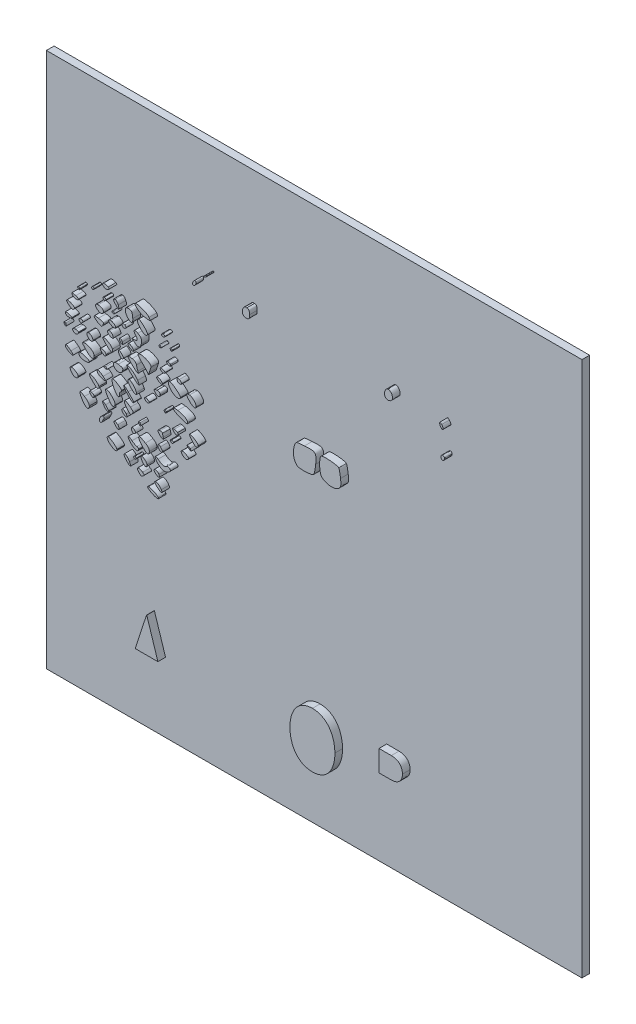
SolidWorks part; units mm, degrees
ref_plane "Plan de face" through (0, 0, 0) normal (0, 0, 1) x (1, 0, 0)
ref_plane "Plan de dessus" through (0, 0, 0) normal (0, 1, 0) x (1, 0, 0)
ref_plane "Plan de droite" through (0, 0, 0) normal (1, 0, 0) x (0, 0, -1)
sketch "Esquisse1" plane through (0, 0, 0) normal (0, 0, 1) x (1, 0, 0)
  line L1 (0, 0) -> (35, 0)
  line L2 (0, 0) -> (0, -35)
  line L3 (0, -35) -> (35, -35)
  line L4 (35, 0) -> (35, -35)
  dimension "D1" = 35
  dimension "D2" = 35
extrude "Boss.-Extru.1" add sketch "Esquisse1" along normal blind 0.5
sketch "Esquisse2" plane through (0, 0, 0) normal (0, 0, -1) x (-1, 0, 0)
  line L0 (-35, 0) -> (0, 0) construction
  line L1 (-35, -35) -> (-35, 0) construction
  line L2 (0, 0) -> (0, -35) construction
  circle A0 centre (-30, -17.5) radius 1
  circle A1 centre (-5, -17.5) radius 1
  dimension "D4" = 2
  dimension "D1" = 17.5
  dimension "D2" = 5
  dimension "D3" = 5
extrude "Boss.-Extru.2" add sketch "Esquisse2" along normal blind 3
chamfer "Chanfrein1" distance 0.5 angle 45 2 edges at (29, -17.5, -3) (4, -17.5, -3)
sketch "Esquisse15" plane through (0, 0, 0.5) normal (0, 0, 1) x (1, 0, 0)
  point P0 (0, 0.001)
  point P1 (0.001, 0.001)
  point P2 (0.001, 0)
ref_plane "Plan7" through (0, 0, 0.5) normal (0, 0, -1) x (-1, 0, 0)
sketch "Esquisse16" plane through (0, 0, 0) normal (0, 0, 1) x (1, 0, 0)
  line L18 (6.2636, -13.0005) -> (6.0872, -13.003)
  line L19 (6.0872, -13.003) -> (6.2675, -13.1533)
  line L37 (7.0433, -28.1853) -> (7.0589, -28.1853)
  line L38 (7.0589, -28.1853) -> (7.7859, -30.4524)
  line L39 (7.7859, -30.4524) -> (6.3006, -30.4524)
  line L40 (6.3006, -30.4524) -> (7.0433, -28.1853)
  line L54 (22.236, -28.1384) -> (23.0412, -28.1384)
  line L55 (23.0412, -29.5221) -> (22.236, -29.5221)
  line L56 (22.236, -29.5221) -> (22.236, -28.1384)
  spline S112 degree 3 poles (7.8123, -21.154) (7.7314, -21.0232) (7.3015, -20.8294) (7.1603, -20.8601) knots 0 0 0 0 1 1 1 1
  spline S113 degree 3 poles (7.1603, -20.8601) (7.0618, -20.8816) (7.0979, -20.9324) (7.3028, -21.0607) knots 0 0 0 0 1 1 1 1
  spline S114 degree 3 poles (7.3028, -21.0607) (7.5848, -21.2371) (7.8992, -21.2947) (7.8123, -21.154) knots 0 0 0 0 1 1 1 1
  spline S115 degree 3 poles (8.0096, -20.6074) (7.9064, -20.4144) (7.6427, -20.2645) (7.5813, -20.3638) knots 0 0 0 0 1 1 1 1
  spline S116 degree 3 poles (7.5813, -20.3638) (7.5356, -20.4378) (7.8945, -20.7624) (8.022, -20.7624) knots 0 0 0 0 1 1 1 1
  spline S117 degree 3 poles (8.022, -20.7624) (8.0608, -20.7624) (8.0553, -20.6926) (8.0096, -20.6074) knots 0 0 0 0 1 1 1 1
  spline S118 degree 3 poles (6.7851, -20.2372) (6.6364, -20.1284) (6.4401, -20.1002) (6.4401, -20.1876) knots 0 0 0 0 1 1 1 1
  spline S119 degree 3 poles (6.4401, -20.1876) (6.4401, -20.2166) (6.4984, -20.3047) (6.5697, -20.3834) knots 0 0 0 0 1 1 1 1
  spline S120 degree 3 poles (6.5697, -20.3834) (6.6725, -20.4971) (6.7225, -20.5073) (6.812, -20.433) knots 0 0 0 0 1 1 1 1
  spline S121 degree 3 poles (6.812, -20.433) (6.9091, -20.3524) (6.9053, -20.325) (6.7851, -20.2372) knots 0 0 0 0 1 1 1 1
  spline S122 degree 3 poles (5.9352, -20.0661) (5.8138, -19.8312) (5.5774, -19.6807) (5.5774, -19.8383) knots 0 0 0 0 1 1 1 1
  spline S123 degree 3 poles (5.5774, -19.8383) (5.5774, -19.9453) (5.889, -20.2919) (5.9852, -20.2919) knots 0 0 0 0 1 1 1 1
  spline S124 degree 3 poles (5.9852, -20.2919) (6.0219, -20.2919) (5.9994, -20.1903) (5.9352, -20.0661) knots 0 0 0 0 1 1 1 1
  spline S125 degree 3 poles (7.8518, -19.8213) (7.7706, -19.6695) (7.5381, -19.5998) (7.5381, -19.7272) knots 0 0 0 0 1 1 1 1
  spline S126 degree 3 poles (7.5381, -19.7272) (7.5381, -19.8259) (7.7158, -19.9781) (7.831, -19.9781) knots 0 0 0 0 1 1 1 1
  spline S127 degree 3 poles (7.831, -19.9781) (7.9115, -19.9781) (7.9163, -19.9417) (7.8518, -19.8213) knots 0 0 0 0 1 1 1 1
  spline S128 degree 3 poles (5.1068, -19.7809) (5.1068, -19.6734) (4.6813, -19.3517) (4.5382, -19.351) knots 0 0 0 0 1 1 1 1
  spline S129 degree 3 poles (4.5382, -19.351) (4.4, -19.3503) (4.4964, -19.5856) (4.6951, -19.7338) knots 0 0 0 0 1 1 1 1
  spline S130 degree 3 poles (4.6951, -19.7338) (4.9526, -19.926) (5.1068, -19.9436) (5.1068, -19.7809) knots 0 0 0 0 1 1 1 1
  spline S131 degree 3 poles (7.0675, -19.6672) (7.0675, -19.5357) (6.8643, -19.3507) (6.7198, -19.3507) knots 0 0 0 0 1 1 1 1
  spline S132 degree 3 poles (6.7198, -19.3507) (6.63, -19.3507) (6.6791, -19.5385) (6.8052, -19.6779) knots 0 0 0 0 1 1 1 1
  spline S133 degree 3 poles (6.8052, -19.6779) (6.9734, -19.8637) (7.0675, -19.8599) (7.0675, -19.6672) knots 0 0 0 0 1 1 1 1
  spline S134 degree 3 poles (6.3617, -19.6644) (6.3617, -19.6213) (6.3264, -19.586) (6.2832, -19.586) knots 0 0 0 0 1 1 1 1
  spline S135 degree 3 poles (6.2832, -19.586) (6.2401, -19.586) (6.2048, -19.6213) (6.2048, -19.6644) knots 0 0 0 0 1 1 1 1
  spline S136 degree 3 poles (6.2048, -19.6644) (6.2048, -19.7076) (6.2401, -19.7428) (6.2832, -19.7428) knots 0 0 0 0 1 1 1 1
  spline S137 degree 3 poles (6.2832, -19.7428) (6.3264, -19.7428) (6.3617, -19.7075) (6.3617, -19.6644) knots 0 0 0 0 1 1 1 1
  spline S138 degree 3 poles (8.539, -19.3307) (8.7003, -19.2016) (8.5056, -19.0192) (8.3261, -19.1313) knots 0 0 0 0 1 1 1 1
  spline S139 degree 3 poles (8.3261, -19.1313) (8.1782, -19.2236) (8.0788, -19.1971) (7.793, -18.9893) knots 0 0 0 0 1 1 1 1
  spline S140 degree 3 poles (7.793, -18.9893) (7.5055, -18.7802) (7.5647, -19.0579) (7.8607, -19.307) knots 0 0 0 0 1 1 1 1
  spline S141 degree 3 poles (7.8607, -19.307) (8.1055, -19.5129) (8.3028, -19.5198) (8.539, -19.3307) knots 0 0 0 0 1 1 1 1
  spline S142 degree 3 poles (6.5185, -19.0762) (6.5185, -19.0115) (6.4704, -18.9586) (6.4115, -18.9586) knots 0 0 0 0 1 1 1 1
  spline S143 degree 3 poles (6.4115, -18.9586) (6.3526, -18.9586) (6.2096, -18.884) (6.0936, -18.7928) knots 0 0 0 0 1 1 1 1
  spline S144 degree 3 poles (6.0936, -18.7928) (5.798, -18.5602) (5.739, -18.6771) (6.0095, -18.9594) knots 0 0 0 0 1 1 1 1
  spline S145 degree 3 poles (6.0095, -18.9594) (6.2487, -19.209) (6.5185, -19.271) (6.5185, -19.0762) knots 0 0 0 0 1 1 1 1
  spline S146 degree 3 poles (7.2244, -18.8398) (7.2244, -18.7014) (7.1483, -18.5961) (6.9695, -18.4871) knots 0 0 0 0 1 1 1 1
  spline S147 degree 3 poles (6.9695, -18.4871) (6.4795, -18.1883) (6.3777, -18.3221) (6.7619, -18.7598) knots 0 0 0 0 1 1 1 1
  spline S148 degree 3 poles (6.7619, -18.7598) (7.0498, -19.0877) (7.2244, -19.1178) (7.2244, -18.8398) knots 0 0 0 0 1 1 1 1
  spline S149 degree 3 poles (4.2049, -18.5664) (4.2984, -18.3856) (4.3032, -18.3311) (4.2258, -18.3311) knots 0 0 0 0 1 1 1 1
  spline S150 degree 3 poles (4.2258, -18.3311) (4.0989, -18.3311) (3.9094, -18.6258) (3.9716, -18.7265) knots 0 0 0 0 1 1 1 1
  spline S151 degree 3 poles (3.9716, -18.7265) (4.0428, -18.8417) (4.0734, -18.8208) (4.2049, -18.5664) knots 0 0 0 0 1 1 1 1
  spline S152 degree 3 poles (5.1628, -18.3535) (5.0974, -18.2881) (4.9984, -18.2496) (4.943, -18.2681) knots 0 0 0 0 1 1 1 1
  spline S153 degree 3 poles (4.943, -18.2681) (4.8728, -18.2915) (4.8988, -18.3583) (5.0284, -18.488) knots 0 0 0 0 1 1 1 1
  spline S154 degree 3 poles (5.0284, -18.488) (5.158, -18.6176) (5.2249, -18.6436) (5.2483, -18.5734) knots 0 0 0 0 1 1 1 1
  spline S155 degree 3 poles (5.2483, -18.5734) (5.2668, -18.518) (5.2283, -18.419) (5.1628, -18.3535) knots 0 0 0 0 1 1 1 1
  spline S156 degree 3 poles (8.0871, -18.4151) (8.0871, -18.3751) (8.0269, -18.2821) (7.9534, -18.2086) knots 0 0 0 0 1 1 1 1
  spline S157 degree 3 poles (7.9534, -18.2086) (7.7935, -18.0487) (7.7056, -18.1942) (7.854, -18.373) knots 0 0 0 0 1 1 1 1
  spline S158 degree 3 poles (7.854, -18.373) (7.9615, -18.5025) (8.0871, -18.5252) (8.0871, -18.4151) knots 0 0 0 0 1 1 1 1
  spline S159 degree 3 poles (3.303, -18.2274) (3.303, -18.1014) (3.2062, -17.9819) (2.9892, -17.8399) knots 0 0 0 0 1 1 1 1
  spline S160 degree 3 poles (2.9892, -17.8399) (2.6678, -17.6294) (2.6082, -17.6622) (2.764, -17.9637) knots 0 0 0 0 1 1 1 1
  spline S161 degree 3 poles (2.764, -17.9637) (2.9922, -18.4054) (3.303, -18.5574) (3.303, -18.2274) knots 0 0 0 0 1 1 1 1
  spline S162 degree 3 poles (6.317, -18.2616) (6.3682, -18.1787) (6.1434, -17.9743) (6.0756, -18.0421) knots 0 0 0 0 1 1 1 1
  spline S163 degree 3 poles (6.0756, -18.0421) (6.0102, -18.1074) (6.1048, -18.3311) (6.1977, -18.3311) knots 0 0 0 0 1 1 1 1
  spline S164 degree 3 poles (6.1977, -18.3311) (6.2397, -18.3311) (6.2933, -18.2998) (6.317, -18.2616) knots 0 0 0 0 1 1 1 1
  spline S165 degree 3 poles (9.7885, -17.9721) (9.8228, -17.8691) (9.4394, -17.6827) (9.331, -17.7497) knots 0 0 0 0 1 1 1 1
  spline S166 degree 3 poles (9.331, -17.7497) (9.2228, -17.8166) (9.4993, -18.1073) (9.6444, -18.0791) knots 0 0 0 0 1 1 1 1
  spline S167 degree 3 poles (9.6444, -18.0791) (9.7081, -18.0668) (9.773, -18.0186) (9.7885, -17.9721) knots 0 0 0 0 1 1 1 1
  spline S168 degree 3 poles (4.5578, -17.8742) (4.5578, -17.8386) (4.4696, -17.7266) (4.3617, -17.6253) knots 0 0 0 0 1 1 1 1
  spline S169 degree 3 poles (4.3617, -17.6253) (4.1425, -17.4193) (4.1008, -17.4978) (4.2878, -17.7647) knots 0 0 0 0 1 1 1 1
  spline S170 degree 3 poles (4.2878, -17.7647) (4.4091, -17.9378) (4.5578, -17.9982) (4.5578, -17.8742) knots 0 0 0 0 1 1 1 1
  spline S171 degree 3 poles (6.6113, -17.5298) (6.5551, -17.4736) (6.5185, -17.4689) (6.5185, -17.5181) knots 0 0 0 0 1 1 1 1
  spline S172 degree 3 poles (6.5185, -17.5181) (6.5185, -17.6228) (6.6113, -17.7155) (6.6636, -17.6632) knots 0 0 0 0 1 1 1 1
  spline S173 degree 3 poles (6.6636, -17.6632) (6.6859, -17.6409) (6.6624, -17.5809) (6.6113, -17.5298) knots 0 0 0 0 1 1 1 1
  spline S174 degree 3 poles (8.1347, -17.5796) (8.1085, -17.5114) (8.0871, -17.4232) (8.0871, -17.3836) knots 0 0 0 0 1 1 1 1
  spline S175 degree 3 poles (8.0871, -17.3836) (8.0871, -17.344) (8.0165, -17.3116) (7.9303, -17.3116) knots 0 0 0 0 1 1 1 1
  spline S176 degree 3 poles (7.9303, -17.3116) (7.7394, -17.3116) (7.7328, -17.372) (7.9032, -17.5603) knots 0 0 0 0 1 1 1 1
  spline S177 degree 3 poles (7.9032, -17.5603) (8.0627, -17.7365) (8.1993, -17.7479) (8.1347, -17.5796) knots 0 0 0 0 1 1 1 1
  spline S178 degree 3 poles (3.6167, -17.5168) (3.6167, -17.4571) (3.5461, -17.3898) (3.4598, -17.3673) knots 0 0 0 0 1 1 1 1
  spline S179 degree 3 poles (3.4598, -17.3673) (3.2832, -17.3211) (3.2565, -17.3906) (3.3971, -17.5311) knots 0 0 0 0 1 1 1 1
  spline S180 degree 3 poles (3.3971, -17.5311) (3.5224, -17.6564) (3.6167, -17.6503) (3.6167, -17.5168) knots 0 0 0 0 1 1 1 1
  spline S181 degree 3 poles (5.716, -17.4684) (5.6199, -17.3144) (5.4205, -17.2509) (5.4205, -17.3743) knots 0 0 0 0 1 1 1 1
  spline S182 degree 3 poles (5.4205, -17.3743) (5.4205, -17.4723) (5.5978, -17.6253) (5.7114, -17.6253) knots 0 0 0 0 1 1 1 1
  spline S183 degree 3 poles (5.7114, -17.6253) (5.7944, -17.6253) (5.7953, -17.5952) (5.716, -17.4684) knots 0 0 0 0 1 1 1 1
  spline S184 degree 3 poles (8.793, -17.5468) (8.793, -17.5037) (8.7379, -17.4684) (8.6707, -17.4684) knots 0 0 0 0 1 1 1 1
  spline S185 degree 3 poles (8.6707, -17.4684) (8.6034, -17.4684) (8.5702, -17.5037) (8.5969, -17.5468) knots 0 0 0 0 1 1 1 1
  spline S186 degree 3 poles (8.5969, -17.5468) (8.6235, -17.59) (8.6786, -17.6253) (8.7192, -17.6253) knots 0 0 0 0 1 1 1 1
  spline S187 degree 3 poles (8.7192, -17.6253) (8.7598, -17.6253) (8.793, -17.59) (8.793, -17.5468) knots 0 0 0 0 1 1 1 1
  spline S188 degree 3 poles (4.983, -17.3386) (5.059, -17.1406) (4.4761, -16.5775) (4.3711, -16.7475) knots 0 0 0 0 1 1 1 1
  spline S189 degree 3 poles (4.3711, -16.7475) (4.3117, -16.8436) (4.708, -17.4684) (4.8284, -17.4684) knots 0 0 0 0 1 1 1 1
  spline S190 degree 3 poles (4.8284, -17.4684) (4.886, -17.4684) (4.9556, -17.41) (4.983, -17.3386) knots 0 0 0 0 1 1 1 1
  spline S191 degree 3 poles (9.891, -17.3508) (9.8373, -17.2861) (9.7535, -17.2342) (9.7049, -17.2356) knots 0 0 0 0 1 1 1 1
  spline S192 degree 3 poles (9.7049, -17.2356) (9.6563, -17.237) (9.685, -17.2899) (9.7687, -17.3533) knots 0 0 0 0 1 1 1 1
  spline S193 degree 3 poles (9.7687, -17.3533) (9.9643, -17.5012) (10.0149, -17.5001) (9.891, -17.3508) knots 0 0 0 0 1 1 1 1
  spline S194 degree 3 poles (5.9899, -16.9454) (5.5762, -16.6067) (5.4424, -16.747) (5.7878, -17.1574) knots 0 0 0 0 1 1 1 1
  spline S195 degree 3 poles (5.7878, -17.1574) (5.9853, -17.3922) (6.0045, -17.3987) (6.1022, -17.265) knots 0 0 0 0 1 1 1 1
  spline S196 degree 3 poles (6.1022, -17.265) (6.1933, -17.1404) (6.1793, -17.1005) (5.9899, -16.9454) knots 0 0 0 0 1 1 1 1
  spline S197 degree 3 poles (2.5797, -16.9129) (2.6011, -16.8013) (2.3103, -16.6057) (2.1228, -16.6057) knots 0 0 0 0 1 1 1 1
  spline S198 degree 3 poles (2.1228, -16.6057) (2.0056, -16.6057) (2.0352, -16.7752) (2.1805, -16.9358) knots 0 0 0 0 1 1 1 1
  spline S199 degree 3 poles (2.1805, -16.9358) (2.3329, -17.1042) (2.5452, -17.092) (2.5797, -16.9129) knots 0 0 0 0 1 1 1 1
  spline S200 degree 3 poles (9.0717, -16.8478) (9.0427, -16.8009) (8.945, -16.7626) (8.8546, -16.7626) knots 0 0 0 0 1 1 1 1
  spline S201 degree 3 poles (8.8546, -16.7626) (8.6945, -16.7626) (8.694, -16.7667) (8.8339, -16.9213) knots 0 0 0 0 1 1 1 1
  spline S202 degree 3 poles (8.8339, -16.9213) (8.9784, -17.081) (9.1778, -17.0195) (9.0717, -16.8478) knots 0 0 0 0 1 1 1 1
  spline S203 degree 3 poles (10.4225, -16.9123) (10.4444, -16.7992) (9.9255, -16.4666) (9.8481, -16.5441) knots 0 0 0 0 1 1 1 1
  spline S204 degree 3 poles (9.8481, -16.5441) (9.825, -16.5671) (9.9001, -16.6978) (10.0151, -16.8344) knots 0 0 0 0 1 1 1 1
  spline S205 degree 3 poles (10.0151, -16.8344) (10.2269, -17.0861) (10.3829, -17.1159) (10.4225, -16.9123) knots 0 0 0 0 1 1 1 1
  spline S206 degree 3 poles (3.9304, -16.8119) (3.9304, -16.6791) (3.4806, -16.3542) (3.3395, -16.385) knots 0 0 0 0 1 1 1 1
  spline S207 degree 3 poles (3.3395, -16.385) (3.2601, -16.4023) (3.3098, -16.4977) (3.5059, -16.7048) knots 0 0 0 0 1 1 1 1
  spline S208 degree 3 poles (3.5059, -16.7048) (3.7721, -16.9859) (3.9304, -17.0259) (3.9304, -16.8119) knots 0 0 0 0 1 1 1 1
  spline S209 degree 3 poles (5.2637, -16.6104) (5.2637, -16.5266) (5.299, -16.4363) (5.3421, -16.4097) knots 0 0 0 0 1 1 1 1
  spline S210 degree 3 poles (5.3421, -16.4097) (5.3852, -16.383) (5.4205, -16.3274) (5.4205, -16.2862) knots 0 0 0 0 1 1 1 1
  spline S211 degree 3 poles (5.4205, -16.2862) (5.4205, -16.2113) (4.9631, -15.9007) (4.8519, -15.9002) knots 0 0 0 0 1 1 1 1
  spline S212 degree 3 poles (4.8519, -15.9002) (4.7305, -15.8995) (4.7995, -16.2525) (4.9696, -16.5023) knots 0 0 0 0 1 1 1 1
  spline S213 degree 3 poles (4.9696, -16.5023) (5.1702, -16.797) (5.2637, -16.8313) (5.2637, -16.6104) knots 0 0 0 0 1 1 1 1
  spline S214 degree 3 poles (6.2048, -16.5586) (6.2048, -16.5328) (6.0442, -16.3486) (5.8478, -16.1494) knots 0 0 0 0 1 1 1 1
  spline S215 degree 3 poles (5.8478, -16.1494) (5.4547, -15.7507) (5.4471, -15.933) (5.8394, -16.3508) knots 0 0 0 0 1 1 1 1
  spline S216 degree 3 poles (5.8394, -16.3508) (6.0625, -16.5884) (6.2048, -16.6694) (6.2048, -16.5586) knots 0 0 0 0 1 1 1 1
  spline S217 degree 3 poles (4.2049, -16.0935) (3.9356, -15.8728) (3.7554, -15.8398) (3.8261, -16.0241) knots 0 0 0 0 1 1 1 1
  spline S218 degree 3 poles (3.8261, -16.0241) (3.8756, -16.1531) (4.1187, -16.2805) (4.3225, -16.2842) knots 0 0 0 0 1 1 1 1
  spline S219 degree 3 poles (4.3225, -16.2842) (4.3939, -16.2855) (4.3476, -16.2105) (4.2049, -16.0935) knots 0 0 0 0 1 1 1 1
  spline S220 degree 3 poles (7.2244, -16.0651) (7.2244, -15.9856) (6.9855, -15.8773) (6.9308, -15.932) knots 0 0 0 0 1 1 1 1
  spline S221 degree 3 poles (6.9308, -15.932) (6.9111, -15.9517) (6.9182, -16.0055) (6.9467, -16.0515) knots 0 0 0 0 1 1 1 1
  spline S222 degree 3 poles (6.9467, -16.0515) (7.0092, -16.1527) (7.2244, -16.1633) (7.2244, -16.0651) knots 0 0 0 0 1 1 1 1
  spline S223 degree 3 poles (8.3224, -16.0567) (8.3224, -16.0135) (8.285, -15.9783) (8.2393, -15.9783) knots 0 0 0 0 1 1 1 1
  spline S224 degree 3 poles (8.2393, -15.9783) (8.1937, -15.9783) (8.1781, -16.0135) (8.2047, -16.0567) knots 0 0 0 0 1 1 1 1
  spline S225 degree 3 poles (8.2047, -16.0567) (8.2314, -16.0998) (8.2688, -16.1351) (8.2878, -16.1351) knots 0 0 0 0 1 1 1 1
  spline S226 degree 3 poles (8.2878, -16.1351) (8.3068, -16.1351) (8.3224, -16.0998) (8.3224, -16.0567) knots 0 0 0 0 1 1 1 1
  spline S227 degree 3 poles (6.3867, -15.9194) (6.3164, -15.72) (6.0375, -15.4293) (5.9166, -15.4293) knots 0 0 0 0 1 1 1 1
  spline S228 degree 3 poles (5.9166, -15.4293) (5.751, -15.4293) (5.7954, -15.5987) (6.0234, -15.8367) knots 0 0 0 0 1 1 1 1
  spline S229 degree 3 poles (6.0234, -15.8367) (6.2622, -16.086) (6.4615, -16.1314) (6.3867, -15.9194) knots 0 0 0 0 1 1 1 1
  spline S230 degree 3 poles (9.7341, -15.9418) (9.7341, -15.7989) (9.4727, -15.6539) (9.0871, -15.5829) knots 0 0 0 0 1 1 1 1
  spline S231 degree 3 poles (9.0871, -15.5829) (8.6359, -15.4998) (8.7131, -15.7013) (9.2047, -15.8903) knots 0 0 0 0 1 1 1 1
  spline S232 degree 3 poles (9.2047, -15.8903) (9.7072, -16.0834) (9.7341, -16.086) (9.7341, -15.9418) knots 0 0 0 0 1 1 1 1
  spline S233 degree 3 poles (2.1026, -15.7013) (1.8737, -15.5) (1.7344, -15.4547) (1.7344, -15.5817) knots 0 0 0 0 1 1 1 1
  spline S234 degree 3 poles (1.7344, -15.5817) (1.7344, -15.6834) (2.0563, -15.9004) (2.2028, -15.8974) knots 0 0 0 0 1 1 1 1
  spline S235 degree 3 poles (2.2028, -15.8974) (2.2844, -15.8957) (2.2523, -15.833) (2.1026, -15.7013) knots 0 0 0 0 1 1 1 1
  spline S236 degree 3 poles (3.303, -15.723) (3.303, -15.597) (2.7398, -15.4145) (2.6436, -15.5093) knots 0 0 0 0 1 1 1 1
  spline S237 degree 3 poles (2.6436, -15.5093) (2.601, -15.5512) (2.6128, -15.6282) (2.6728, -15.7004) knots 0 0 0 0 1 1 1 1
  spline S238 degree 3 poles (2.6728, -15.7004) (2.7944, -15.8469) (3.303, -15.8651) (3.303, -15.723) knots 0 0 0 0 1 1 1 1
  spline S239 degree 3 poles (4.4794, -15.5553) (4.4794, -15.5383) (4.4264, -15.5042) (4.3617, -15.4793) knots 0 0 0 0 1 1 1 1
  spline S240 degree 3 poles (4.3617, -15.4793) (4.297, -15.4545) (4.2441, -15.4684) (4.2441, -15.5101) knots 0 0 0 0 1 1 1 1
  spline S241 degree 3 poles (4.2441, -15.5101) (4.2441, -15.5519) (4.297, -15.5861) (4.3617, -15.5861) knots 0 0 0 0 1 1 1 1
  spline S242 degree 3 poles (4.3617, -15.5861) (4.4265, -15.5861) (4.4794, -15.5722) (4.4794, -15.5553) knots 0 0 0 0 1 1 1 1
  spline S243 degree 3 poles (3.6167, -15.2352) (3.6167, -15.0129) (3.248, -14.7763) (2.9643, -14.8167) knots 0 0 0 0 1 1 1 1
  spline S244 degree 3 poles (2.9643, -14.8167) (2.8024, -14.8397) (2.8079, -14.8568) (3.0677, -15.1337) knots 0 0 0 0 1 1 1 1
  spline S245 degree 3 poles (3.0677, -15.1337) (3.392, -15.4794) (3.6167, -15.521) (3.6167, -15.2352) knots 0 0 0 0 1 1 1 1
  spline S246 degree 3 poles (6.4641, -15.1886) (6.3099, -14.9266) (5.8377, -14.5927) (5.7497, -14.6835) knots 0 0 0 0 1 1 1 1
  spline S247 degree 3 poles (5.7497, -14.6835) (5.6936, -14.7414) (6.4229, -15.4293) (6.5404, -15.4293) knots 0 0 0 0 1 1 1 1
  spline S248 degree 3 poles (6.5404, -15.4293) (6.5764, -15.4293) (6.5421, -15.3209) (6.4641, -15.1886) knots 0 0 0 0 1 1 1 1
  spline S249 degree 3 poles (7.9302, -15.2724) (7.9302, -15.1574) (7.878, -15.1155) (7.7342, -15.1155) knots 0 0 0 0 1 1 1 1
  spline S250 degree 3 poles (7.7342, -15.1155) (7.5201, -15.1155) (7.486, -15.1889) (7.6322, -15.3351) knots 0 0 0 0 1 1 1 1
  spline S251 degree 3 poles (7.6322, -15.3351) (7.7765, -15.4795) (7.9302, -15.4471) (7.9302, -15.2724) knots 0 0 0 0 1 1 1 1
  spline S252 degree 3 poles (5.4616, -15.1881) (5.525, -14.9883) (5.5103, -14.9727) (5.2003, -14.9107) knots 0 0 0 0 1 1 1 1
  spline S253 degree 3 poles (5.2003, -14.9107) (4.9181, -14.8543) (4.7819, -15.0307) (4.9508, -15.2342) knots 0 0 0 0 1 1 1 1
  spline S254 degree 3 poles (4.9508, -15.2342) (5.0954, -15.4085) (5.4004, -15.3809) (5.4616, -15.1881) knots 0 0 0 0 1 1 1 1
  spline S255 degree 3 poles (4.401, -14.7679) (4.401, -14.6456) (4.1081, -14.5195) (4.0226, -14.605) knots 0 0 0 0 1 1 1 1
  spline S256 degree 3 poles (4.0226, -14.605) (3.9688, -14.6588) (4.2222, -14.8803) (4.3375, -14.8803) knots 0 0 0 0 1 1 1 1
  spline S257 degree 3 poles (4.3375, -14.8803) (4.3724, -14.8803) (4.401, -14.8297) (4.401, -14.7679) knots 0 0 0 0 1 1 1 1
  spline S258 degree 3 poles (9.2635, -14.7631) (9.2635, -14.6251) (8.648, -14.1577) (8.5479, -14.2196) knots 0 0 0 0 1 1 1 1
  spline S259 degree 3 poles (8.5479, -14.2196) (8.4241, -14.2961) (8.4758, -14.4918) (8.6718, -14.6877) knots 0 0 0 0 1 1 1 1
  spline S260 degree 3 poles (8.6718, -14.6877) (8.8866, -14.9025) (9.2635, -14.9505) (9.2635, -14.7631) knots 0 0 0 0 1 1 1 1
  spline S261 degree 3 poles (10.2831, -14.78) (10.2831, -14.5839) (10.0378, -14.3312) (9.8473, -14.3312) knots 0 0 0 0 1 1 1 1
  spline S262 degree 3 poles (9.8473, -14.3312) (9.6055, -14.3312) (9.6056, -14.4112) (9.848, -14.6727) knots 0 0 0 0 1 1 1 1
  spline S263 degree 3 poles (9.848, -14.6727) (10.0509, -14.8916) (10.2831, -14.9489) (10.2831, -14.78) knots 0 0 0 0 1 1 1 1
  spline S264 degree 3 poles (6.4776, -14.6645) (6.4459, -14.589) (6.4034, -14.4516) (6.3832, -14.3591) knots 0 0 0 0 1 1 1 1
  spline S265 degree 3 poles (6.3832, -14.3591) (6.3588, -14.2471) (6.2663, -14.1749) (6.1063, -14.1429) knots 0 0 0 0 1 1 1 1
  spline S266 degree 3 poles (6.1063, -14.1429) (5.7488, -14.0714) (5.745, -14.1491) (6.09, -14.4814) knots 0 0 0 0 1 1 1 1
  spline S267 degree 3 poles (6.09, -14.4814) (6.4327, -14.8116) (6.5659, -14.8746) (6.4776, -14.6645) knots 0 0 0 0 1 1 1 1
  spline S268 degree 3 poles (2.5971, -14.4) (2.5971, -14.3622) (2.5089, -14.3312) (2.401, -14.3312) knots 0 0 0 0 1 1 1 1
  spline S269 degree 3 poles (2.401, -14.3312) (2.1878, -14.3312) (2.1528, -14.4046) (2.2972, -14.5489) knots 0 0 0 0 1 1 1 1
  spline S270 degree 3 poles (2.2972, -14.5489) (2.3934, -14.6451) (2.5971, -14.5439) (2.5971, -14.4) knots 0 0 0 0 1 1 1 1
  spline S271 degree 3 poles (8.0871, -14.5692) (8.0871, -14.4685) (7.7741, -14.3044) (7.708, -14.3705) knots 0 0 0 0 1 1 1 1
  spline S272 degree 3 poles (7.708, -14.3705) (7.6794, -14.3991) (7.7244, -14.4725) (7.8081, -14.5337) knots 0 0 0 0 1 1 1 1
  spline S273 degree 3 poles (7.8081, -14.5337) (7.9852, -14.6632) (8.0871, -14.6762) (8.0871, -14.5692) knots 0 0 0 0 1 1 1 1
  spline S274 degree 3 poles (7.3347, -14.0135) (7.4226, -13.8053) (6.607, -13.4972) (6.486, -13.6929) knots 0 0 0 0 1 1 1 1
  spline S275 degree 3 poles (6.486, -13.6929) (6.463, -13.7301) (6.6021, -13.9085) (6.7951, -14.0894) knots 0 0 0 0 1 1 1 1
  spline S276 degree 3 poles (6.7951, -14.0894) (6.9881, -14.2703) (7.1496, -14.4604) (7.154, -14.512) knots 0 0 0 0 1 1 1 1
  spline S277 degree 3 poles (7.154, -14.512) (7.1584, -14.5635) (7.1893, -14.4998) (7.2227, -14.3704) knots 0 0 0 0 1 1 1 1
  spline S278 degree 3 poles (7.2227, -14.3704) (7.2561, -14.241) (7.3065, -14.0804) (7.3347, -14.0135) knots 0 0 0 0 1 1 1 1
  spline S279 degree 3 poles (1.7488, -14.3142) (1.6925, -14.2579) (1.656, -14.2533) (1.656, -14.3024) knots 0 0 0 0 1 1 1 1
  spline S280 degree 3 poles (1.656, -14.3024) (1.656, -14.4071) (1.7487, -14.4999) (1.8011, -14.4475) knots 0 0 0 0 1 1 1 1
  spline S281 degree 3 poles (1.8011, -14.4475) (1.8233, -14.4253) (1.7999, -14.3653) (1.7488, -14.3142) knots 0 0 0 0 1 1 1 1
  spline S282 degree 3 poles (3.5382, -14.3861) (3.5382, -14.2549) (3.3792, -14.0959) (3.2481, -14.0959) knots 0 0 0 0 1 1 1 1
  spline S283 degree 3 poles (3.2481, -14.0959) (3.1201, -14.0959) (3.1156, -14.2693) (3.2402, -14.3939) knots 0 0 0 0 1 1 1 1
  spline S284 degree 3 poles (3.2402, -14.3939) (3.3648, -14.5186) (3.5382, -14.514) (3.5382, -14.3861) knots 0 0 0 0 1 1 1 1
  spline S285 degree 3 poles (4.8141, -14.2463) (4.7674, -14.0678) (4.2824, -13.7954) (4.1863, -13.8936) knots 0 0 0 0 1 1 1 1
  spline S286 degree 3 poles (4.1863, -13.8936) (4.116, -13.9654) (4.7076, -14.5017) (4.7965, -14.4468) knots 0 0 0 0 1 1 1 1
  spline S287 degree 3 poles (4.7965, -14.4468) (4.8297, -14.4262) (4.8376, -14.336) (4.8141, -14.2463) knots 0 0 0 0 1 1 1 1
  spline S288 degree 3 poles (5.5317, -14.4201) (5.5815, -14.3395) (5.2831, -14.0503) (5.2176, -14.1158) knots 0 0 0 0 1 1 1 1
  spline S289 degree 3 poles (5.2176, -14.1158) (5.1583, -14.1752) (5.3272, -14.4881) (5.4187, -14.4881) knots 0 0 0 0 1 1 1 1
  spline S290 degree 3 poles (5.4187, -14.4881) (5.4577, -14.4881) (5.5086, -14.4575) (5.5317, -14.4201) knots 0 0 0 0 1 1 1 1
  spline S291 degree 3 poles (9.342, -13.9418) (9.342, -13.9002) (9.2714, -13.8284) (9.1851, -13.7822) knots 0 0 0 0 1 1 1 1
  spline S292 degree 3 poles (9.1851, -13.7822) (9.0638, -13.7173) (9.0282, -13.7226) (9.0282, -13.8056) knots 0 0 0 0 1 1 1 1
  spline S293 degree 3 poles (9.0282, -13.8056) (9.0282, -13.8646) (9.0518, -13.9364) (9.0805, -13.9652) knots 0 0 0 0 1 1 1 1
  spline S294 degree 3 poles (9.0805, -13.9652) (9.1595, -14.0442) (9.342, -14.0279) (9.342, -13.9418) knots 0 0 0 0 1 1 1 1
  spline S295 degree 3 poles (8.244, -13.869) (8.244, -13.7895) (8.0051, -13.6812) (7.9504, -13.7359) knots 0 0 0 0 1 1 1 1
  spline S296 degree 3 poles (7.9504, -13.7359) (7.9307, -13.7556) (7.9378, -13.8094) (7.9662, -13.8554) knots 0 0 0 0 1 1 1 1
  spline S297 degree 3 poles (7.9662, -13.8554) (8.0288, -13.9567) (8.244, -13.9672) (8.244, -13.869) knots 0 0 0 0 1 1 1 1
  spline S298 degree 3 poles (2.1618, -13.791) (2.0466, -13.6834) (1.7344, -13.6062) (1.7344, -13.6854) knots 0 0 0 0 1 1 1 1
  spline S299 degree 3 poles (1.7344, -13.6854) (1.7344, -13.8052) (1.8304, -13.8606) (2.0376, -13.8606) knots 0 0 0 0 1 1 1 1
  spline S300 degree 3 poles (2.0376, -13.8606) (2.157, -13.8606) (2.2066, -13.8328) (2.1618, -13.791) knots 0 0 0 0 1 1 1 1
  spline S301 degree 3 poles (2.8683, -13.7092) (2.9263, -13.6153) (2.7787, -13.5224) (2.6743, -13.5869) knots 0 0 0 0 1 1 1 1
  spline S302 degree 3 poles (2.6743, -13.5869) (2.5865, -13.6411) (2.6441, -13.7822) (2.754, -13.7822) knots 0 0 0 0 1 1 1 1
  spline S303 degree 3 poles (2.754, -13.7822) (2.792, -13.7822) (2.8434, -13.7493) (2.8683, -13.7092) knots 0 0 0 0 1 1 1 1
  spline S304 degree 3 poles (5.4532, -13.5189) (5.4028, -13.3875) (5.2637, -13.339) (5.2637, -13.4528) knots 0 0 0 0 1 1 1 1
  spline S305 degree 3 poles (5.2637, -13.4528) (5.2637, -13.5291) (5.4386, -13.7118) (5.476, -13.6745) knots 0 0 0 0 1 1 1 1
  spline S306 degree 3 poles (5.476, -13.6745) (5.4906, -13.6598) (5.4804, -13.5898) (5.4532, -13.5189) knots 0 0 0 0 1 1 1 1
  spline S307 degree 3 poles (6.1871, -13.6113) (6.1416, -13.4748) (5.9082, -13.3468) (5.8362, -13.4188) knots 0 0 0 0 1 1 1 1
  spline S308 degree 3 poles (5.8362, -13.4188) (5.8018, -13.4532) (5.8422, -13.5314) (5.9258, -13.5925) knots 0 0 0 0 1 1 1 1
  spline S309 degree 3 poles (5.9258, -13.5925) (6.1109, -13.7278) (6.2287, -13.7363) (6.1871, -13.6113) knots 0 0 0 0 1 1 1 1
  spline S310 degree 3 poles (4.8715, -13.5925) (4.8715, -13.4508) (4.7508, -13.3116) (4.6279, -13.3116) knots 0 0 0 0 1 1 1 1
  spline S311 degree 3 poles (4.6279, -13.3116) (4.4578, -13.3116) (4.4372, -13.3949) (4.5735, -13.5312) knots 0 0 0 0 1 1 1 1
  spline S312 degree 3 poles (4.5735, -13.5312) (4.6625, -13.6202) (4.8715, -13.6632) (4.8715, -13.5925) knots 0 0 0 0 1 1 1 1
  spline S313 degree 3 poles (8.5935, -13.2278) (8.5687, -13.1876) (8.4932, -13.1548) (8.4258, -13.1548) knots 0 0 0 0 1 1 1 1
  spline S314 degree 3 poles (8.4258, -13.1548) (8.3261, -13.1548) (8.3213, -13.1766) (8.4001, -13.2715) knots 0 0 0 0 1 1 1 1
  spline S315 degree 3 poles (8.4001, -13.2715) (8.5014, -13.3936) (8.6721, -13.3549) (8.5935, -13.2278) knots 0 0 0 0 1 1 1 1
  spline S316 degree 3 poles (2.3403, -13.1802) (2.3736, -13.0802) (1.9093, -12.8752) (1.8299, -12.9549) knots 0 0 0 0 1 1 1 1
  spline S317 degree 3 poles (1.8299, -12.9549) (1.7595, -13.0255) (2.1208, -13.3266) (2.2315, -13.2897) knots 0 0 0 0 1 1 1 1
  spline S318 degree 3 poles (2.2315, -13.2897) (2.2762, -13.2748) (2.3252, -13.2255) (2.3403, -13.1802) knots 0 0 0 0 1 1 1 1
  spline S319 degree 3 poles (4.1983, -13.1827) (4.2607, -13.0202) (4.2643, -13.023) (3.9007, -12.955) knots 0 0 0 0 1 1 1 1
  spline S320 degree 3 poles (3.9007, -12.955) (3.6593, -12.9099) (3.6039, -12.9206) (3.6324, -13.0068) knots 0 0 0 0 1 1 1 1
  spline S321 degree 3 poles (3.6324, -13.0068) (3.665, -13.1055) (3.9753, -13.3076) (4.0985, -13.3104) knots 0 0 0 0 1 1 1 1
  spline S322 degree 3 poles (4.0985, -13.3104) (4.1262, -13.311) (4.1712, -13.2536) (4.1983, -13.1827) knots 0 0 0 0 1 1 1 1
  spline S323 degree 3 poles (6.6984, -13.0171) (6.7502, -12.7461) (6.706, -12.6486) (6.4753, -12.5251) knots 0 0 0 0 1 1 1 1
  spline S324 degree 3 poles (6.4753, -12.5251) (6.234, -12.396) (6.1379, -12.4802) (6.3099, -12.6702) knots 0 0 0 0 1 1 1 1
  spline S325 degree 3 poles (6.3099, -12.6702) (6.4904, -12.8697) (6.4725, -12.9974) (6.2636, -13.0005) knots 0 0 0 0 1 1 1 1
  spline S326 degree 3 poles (6.2675, -13.1533) (6.4892, -13.3382) (6.6465, -13.2885) (6.6984, -13.0171) knots 0 0 0 0 1 1 1 1
  spline S327 degree 3 poles (5.0284, -12.9351) (5.0284, -12.8243) (4.8445, -12.6842) (4.699, -12.6842) knots 0 0 0 0 1 1 1 1
  spline S328 degree 3 poles (4.699, -12.6842) (4.519, -12.6842) (4.5169, -12.8094) (4.6951, -12.9132) knots 0 0 0 0 1 1 1 1
  spline S329 degree 3 poles (4.6951, -12.9132) (4.8613, -13.0099) (5.0284, -13.0209) (5.0284, -12.9351) knots 0 0 0 0 1 1 1 1
  spline S330 degree 3 poles (5.6954, -12.6051) (5.7222, -12.5617) (5.6875, -12.5044) (5.6182, -12.4778) knots 0 0 0 0 1 1 1 1
  spline S331 degree 3 poles (5.6182, -12.4778) (5.468, -12.4202) (5.3843, -12.4837) (5.4565, -12.6005) knots 0 0 0 0 1 1 1 1
  spline S332 degree 3 poles (5.4565, -12.6005) (5.5217, -12.7059) (5.6318, -12.708) (5.6954, -12.6051) knots 0 0 0 0 1 1 1 1
  spline S333 degree 3 poles (2.5971, -12.5365) (2.5971, -12.4983) (2.5177, -12.4459) (2.4206, -12.4199) knots 0 0 0 0 1 1 1 1
  spline S334 degree 3 poles (2.4206, -12.4199) (2.1459, -12.3463) (2.0995, -12.361) (2.205, -12.4881) knots 0 0 0 0 1 1 1 1
  spline S335 degree 3 poles (2.205, -12.4881) (2.3102, -12.6149) (2.5971, -12.6503) (2.5971, -12.5365) knots 0 0 0 0 1 1 1 1
  spline S336 degree 3 poles (4.2188, -12.4802) (4.2751, -12.3334) (4.1221, -12.2165) (3.8716, -12.2148) knots 0 0 0 0 1 1 1 1
  spline S337 degree 3 poles (3.8716, -12.2148) (3.6609, -12.2133) (3.6417, -12.3518) (3.8324, -12.4966) knots 0 0 0 0 1 1 1 1
  spline S338 degree 3 poles (3.8324, -12.4966) (4.0181, -12.6375) (4.1607, -12.6315) (4.2188, -12.4802) knots 0 0 0 0 1 1 1 1
  spline S339 degree 3 poles (8.0087, -12.5712) (8.0087, -12.5521) (7.9734, -12.5148) (7.9302, -12.4881) knots 0 0 0 0 1 1 1 1
  spline S340 degree 3 poles (7.9302, -12.4881) (7.8871, -12.4614) (7.8518, -12.477) (7.8518, -12.5227) knots 0 0 0 0 1 1 1 1
  spline S341 degree 3 poles (7.8518, -12.5227) (7.8518, -12.5684) (7.8871, -12.6057) (7.9302, -12.6057) knots 0 0 0 0 1 1 1 1
  spline S342 degree 3 poles (7.9302, -12.6057) (7.9734, -12.6057) (8.0087, -12.5902) (8.0087, -12.5712) knots 0 0 0 0 1 1 1 1
  spline S343 degree 3 poles (8.7145, -12.3705) (8.7145, -12.3273) (8.6772, -12.292) (8.6315, -12.292) knots 0 0 0 0 1 1 1 1
  spline S344 degree 3 poles (8.6315, -12.292) (8.5858, -12.292) (8.5702, -12.3273) (8.5969, -12.3705) knots 0 0 0 0 1 1 1 1
  spline S345 degree 3 poles (8.5969, -12.3705) (8.6235, -12.4136) (8.6609, -12.4489) (8.6799, -12.4489) knots 0 0 0 0 1 1 1 1
  spline S346 degree 3 poles (8.6799, -12.4489) (8.699, -12.4489) (8.7145, -12.4136) (8.7145, -12.3705) knots 0 0 0 0 1 1 1 1
  spline S347 degree 3 poles (7.108, -12.2901) (7.1728, -12.1851) (6.6255, -11.6377) (6.5205, -11.7026) knots 0 0 0 0 1 1 1 1
  spline S348 degree 3 poles (6.5205, -11.7026) (6.3897, -11.7835) (6.4273, -11.927) (6.6393, -12.1556) knots 0 0 0 0 1 1 1 1
  spline S349 degree 3 poles (6.6393, -12.1556) (6.8459, -12.3784) (7.0221, -12.4289) (7.108, -12.2901) knots 0 0 0 0 1 1 1 1
  spline S350 degree 3 poles (4.95, -12.179) (4.95, -12.16) (4.9147, -12.1226) (4.8715, -12.096) knots 0 0 0 0 1 1 1 1
  spline S351 degree 3 poles (4.8715, -12.096) (4.8284, -12.0693) (4.7931, -12.0849) (4.7931, -12.1306) knots 0 0 0 0 1 1 1 1
  spline S352 degree 3 poles (4.7931, -12.1306) (4.7931, -12.1763) (4.8284, -12.2136) (4.8715, -12.2136) knots 0 0 0 0 1 1 1 1
  spline S353 degree 3 poles (4.8715, -12.2136) (4.9147, -12.2136) (4.95, -12.1981) (4.95, -12.179) knots 0 0 0 0 1 1 1 1
  spline S354 degree 3 poles (6.1432, -11.8525) (6.1076, -11.4911) (6.0654, -11.4293) (5.8544, -11.4293) knots 0 0 0 0 1 1 1 1
  spline S355 degree 3 poles (5.8544, -11.4293) (5.6949, -11.4293) (5.6558, -11.4679) (5.6558, -11.6254) knots 0 0 0 0 1 1 1 1
  spline S356 degree 3 poles (5.6558, -11.6254) (5.6558, -11.8443) (5.9285, -12.1629) (6.0725, -12.1123) knots 0 0 0 0 1 1 1 1
  spline S357 degree 3 poles (6.0725, -12.1123) (6.1237, -12.0943) (6.1555, -11.9774) (6.1432, -11.8525) knots 0 0 0 0 1 1 1 1
  spline S358 degree 3 poles (2.6755, -11.8999) (2.6755, -11.8568) (2.6382, -11.8215) (2.5925, -11.8215) knots 0 0 0 0 1 1 1 1
  spline S359 degree 3 poles (2.5925, -11.8215) (2.5468, -11.8215) (2.5312, -11.8568) (2.5579, -11.8999) knots 0 0 0 0 1 1 1 1
  spline S360 degree 3 poles (2.5579, -11.8999) (2.5846, -11.9431) (2.6219, -11.9783) (2.6409, -11.9783) knots 0 0 0 0 1 1 1 1
  spline S361 degree 3 poles (2.6409, -11.9783) (2.66, -11.9783) (2.6755, -11.943) (2.6755, -11.8999) knots 0 0 0 0 1 1 1 1
  spline S362 degree 3 poles (8.244, -11.8215) (8.244, -11.7783) (8.191, -11.743) (8.1263, -11.743) knots 0 0 0 0 1 1 1 1
  spline S363 degree 3 poles (8.1263, -11.743) (8.0616, -11.743) (8.0087, -11.7783) (8.0087, -11.8215) knots 0 0 0 0 1 1 1 1
  spline S364 degree 3 poles (8.0087, -11.8215) (8.0087, -11.8646) (8.0616, -11.8999) (8.1263, -11.8999) knots 0 0 0 0 1 1 1 1
  spline S365 degree 3 poles (8.1263, -11.8999) (8.191, -11.8999) (8.244, -11.8646) (8.244, -11.8215) knots 0 0 0 0 1 1 1 1
  spline S366 degree 3 poles (5.1894, -11.558) (5.1461, -11.4441) (5.0569, -11.351) (4.9911, -11.351) knots 0 0 0 0 1 1 1 1
  spline S367 degree 3 poles (4.9911, -11.351) (4.8278, -11.351) (4.8409, -11.4259) (5.0418, -11.6397) knots 0 0 0 0 1 1 1 1
  spline S368 degree 3 poles (5.0418, -11.6397) (5.2481, -11.8594) (5.2943, -11.8338) (5.1894, -11.558) knots 0 0 0 0 1 1 1 1
  spline S369 degree 3 poles (4.401, -11.6647) (4.401, -11.6216) (4.3459, -11.5863) (4.2787, -11.5863) knots 0 0 0 0 1 1 1 1
  spline S370 degree 3 poles (4.2787, -11.5863) (4.2114, -11.5863) (4.1782, -11.6216) (4.2049, -11.6647) knots 0 0 0 0 1 1 1 1
  spline S371 degree 3 poles (4.2049, -11.6647) (4.2316, -11.7079) (4.2866, -11.7432) (4.3272, -11.7432) knots 0 0 0 0 1 1 1 1
  spline S372 degree 3 poles (4.3272, -11.7432) (4.3678, -11.7432) (4.401, -11.7079) (4.401, -11.6647) knots 0 0 0 0 1 1 1 1
  spline S373 degree 3 poles (3.6167, -11.4294) (3.6167, -11.3863) (3.5814, -11.351) (3.5382, -11.351) knots 0 0 0 0 1 1 1 1
  spline S374 degree 3 poles (3.5382, -11.351) (3.4951, -11.351) (3.4598, -11.3863) (3.4598, -11.4294) knots 0 0 0 0 1 1 1 1
  spline S375 degree 3 poles (3.4598, -11.4294) (3.4598, -11.4726) (3.4951, -11.5079) (3.5382, -11.5079) knots 0 0 0 0 1 1 1 1
  spline S376 degree 3 poles (3.5382, -11.5079) (3.5814, -11.5079) (3.6167, -11.4726) (3.6167, -11.4294) knots 0 0 0 0 1 1 1 1
  spline S377 degree 3 poles (7.2048, -11.253) (7.0903, -11.0805) (6.3965, -10.8195) (6.3024, -10.9135) knots 0 0 0 0 1 1 1 1
  spline S378 degree 3 poles (6.3024, -10.9135) (6.211, -11.005) (6.6222, -11.3433) (6.8615, -11.3734) knots 0 0 0 0 1 1 1 1
  spline S379 degree 3 poles (6.8615, -11.3734) (6.9964, -11.3904) (7.1552, -11.41) (7.2143, -11.4169) knots 0 0 0 0 1 1 1 1
  spline S380 degree 3 poles (7.2143, -11.4169) (7.3021, -11.4271) (7.3003, -11.3969) (7.2048, -11.253) knots 0 0 0 0 1 1 1 1
  spline S381 degree 3 poles (4.5419, -10.869) (4.4027, -10.7806) (4.1657, -10.7854) (4.1657, -10.8765) knots 0 0 0 0 1 1 1 1
  spline S382 degree 3 poles (4.1657, -10.8765) (4.1657, -11.0108) (4.43, -11.1109) (4.5411, -11.0186) knots 0 0 0 0 1 1 1 1
  spline S383 degree 3 poles (4.5411, -11.0186) (4.625, -10.949) (4.6252, -10.9218) (4.5419, -10.869) knots 0 0 0 0 1 1 1 1
  spline S384 degree 3 poles (26.5178, -9.5817) (26.5178, -9.5196) (26.4649, -9.4687) (26.4002, -9.4687) knots 0 0 0 0 1 1 1 1
  spline S385 degree 3 poles (26.4002, -9.4687) (26.282, -9.4687) (26.2389, -9.6343) (26.3326, -9.728) knots 0 0 0 0 1 1 1 1
  spline S386 degree 3 poles (26.3326, -9.728) (26.4058, -9.8012) (26.5178, -9.7128) (26.5178, -9.5817) knots 0 0 0 0 1 1 1 1
  spline S387 degree 3 poles (26.3308, -7.758) (26.2212, -7.6483) (26.2041, -7.6472) (26.2041, -7.75) knots 0 0 0 0 1 1 1 1
  spline S388 degree 3 poles (26.2041, -7.75) (26.2041, -7.9112) (26.3876, -8.0947) (26.4279, -7.9738) knots 0 0 0 0 1 1 1 1
  spline S389 degree 3 poles (26.4279, -7.9738) (26.4442, -7.9248) (26.4006, -7.8277) (26.3308, -7.758) knots 0 0 0 0 1 1 1 1
  spline S390 degree 3 poles (10.2561, -7.8576) (10.3195, -7.692) (10.2135, -7.6027) (10.1232, -7.7456) knots 0 0 0 0 1 1 1 1
  spline S391 degree 3 poles (10.1232, -7.7456) (10.0272, -7.8974) (10.0291, -7.9786) (10.1287, -7.9786) knots 0 0 0 0 1 1 1 1
  spline S392 degree 3 poles (10.1287, -7.9786) (10.1732, -7.9786) (10.2305, -7.9241) (10.2561, -7.8576) knots 0 0 0 0 1 1 1 1
  spline S393 degree 3 poles (10.9518, -7.0526) (10.9277, -7.0284) (10.8644, -7.0525) (10.8112, -7.1061) knots 0 0 0 0 1 1 1 1
  spline S394 degree 3 poles (10.8112, -7.1061) (10.7343, -7.1836) (10.7433, -7.1926) (10.8551, -7.15) knots 0 0 0 0 1 1 1 1
  spline S395 degree 3 poles (10.8551, -7.15) (10.9324, -7.1206) (10.976, -7.0767) (10.9518, -7.0526) knots 0 0 0 0 1 1 1 1
  spline S425 degree 3 poles (17.9635, -14.7694) (18.0141, -14.7084) (18.0758, -14.4164) (18.1006, -14.1206) knots 0 0 0 0 1 1 1 1
  spline S426 degree 3 poles (18.1006, -14.1206) (18.1573, -13.4442) (18.1129, -13.4037) (17.366, -13.4504) knots 0 0 0 0 1 1 1 1
  spline S427 degree 3 poles (17.366, -13.4504) (16.8205, -13.4846) (16.7993, -13.4936) (16.7189, -13.7242) knots 0 0 0 0 1 1 1 1
  spline S428 degree 3 poles (16.7189, -13.7242) (16.5671, -14.1595) (16.6495, -14.6514) (16.9024, -14.8203) knots 0 0 0 0 1 1 1 1
  spline S429 degree 3 poles (16.9024, -14.8203) (17.0609, -14.926) (17.8655, -14.8875) (17.9635, -14.7694) knots 0 0 0 0 1 1 1 1
  spline S430 degree 3 poles (19.6167, -14.7228) (19.7521, -14.5875) (19.7671, -14.5021) (19.7237, -14.115) knots 0 0 0 0 1 1 1 1
  spline S431 degree 3 poles (19.7237, -14.115) (19.6959, -13.8673) (19.6424, -13.6254) (19.6048, -13.5774) knots 0 0 0 0 1 1 1 1
  spline S432 degree 3 poles (19.6048, -13.5774) (19.5099, -13.4563) (18.5847, -13.3807) (18.4604, -13.4839) knots 0 0 0 0 1 1 1 1
  spline S433 degree 3 poles (18.4604, -13.4839) (18.301, -13.6162) (18.3301, -14.5151) (18.4985, -14.6618) knots 0 0 0 0 1 1 1 1
  spline S434 degree 3 poles (18.4985, -14.6618) (18.8039, -14.9279) (19.3802, -14.9593) (19.6167, -14.7228) knots 0 0 0 0 1 1 1 1
  spline S440 degree 3 poles (13.7732, -7.8217) (13.7732, -7.5968) (13.7413, -7.5427) (13.5968, -7.5222) knots 0 0 0 0 1 1 1 1
  spline S441 degree 3 poles (13.5968, -7.5222) (13.4657, -7.5036) (13.3999, -7.5513) (13.3403, -7.7082) knots 0 0 0 0 1 1 1 1
  spline S442 degree 3 poles (13.3403, -7.7082) (13.2424, -7.9655) (13.3661, -8.1544) (13.6095, -8.1196) knots 0 0 0 0 1 1 1 1
  spline S443 degree 3 poles (13.6095, -8.1196) (13.7398, -8.101) (13.7732, -8.0403) (13.7732, -7.8217) knots 0 0 0 0 1 1 1 1
  spline S449 degree 3 poles (23.0689, -8.0155) (23.2061, -7.8501) (23.0483, -7.508) (22.8348, -7.508) knots 0 0 0 0 1 1 1 1
  spline S450 degree 3 poles (22.8348, -7.508) (22.6663, -7.508) (22.5435, -7.806) (22.6247, -8.0176) knots 0 0 0 0 1 1 1 1
  spline S451 degree 3 poles (22.6247, -8.0176) (22.6833, -8.1703) (22.9414, -8.1691) (23.0689, -8.0155) knots 0 0 0 0 1 1 1 1
  spline S472 degree 3 poles (17.8844, -31.6406) (16.8916, -31.6406) (16.4147, -30.7963) (16.4147, -29.8426) knots 0 0 0 0 1 1 1 1
  spline S473 degree 3 poles (16.4147, -29.8426) (16.4147, -28.8967) (16.9072, -28.0446) (17.8844, -28.0446) knots 0 0 0 0 1 1 1 1
  spline S474 degree 3 poles (17.8844, -28.0446) (18.8616, -28.0446) (19.3541, -28.8967) (19.3541, -29.8426) knots 0 0 0 0 1 1 1 1
  spline S475 degree 3 poles (19.3541, -29.8426) (19.3541, -30.7963) (18.8772, -31.6406) (17.8844, -31.6406) knots 0 0 0 0 1 1 1 1
  spline S488 degree 3 poles (23.0412, -28.1384) (23.4711, -28.1384) (23.7682, -28.3808) (23.7682, -28.8263) knots 0 0 0 0 1 1 1 1
  spline S489 degree 3 poles (23.7682, -28.8263) (23.7682, -29.2641) (23.4711, -29.5221) (23.0412, -29.5221) knots 0 0 0 0 1 1 1 1
extrude "Boss.-Extru.3" add sketch "Esquisse16" along normal blind 1
